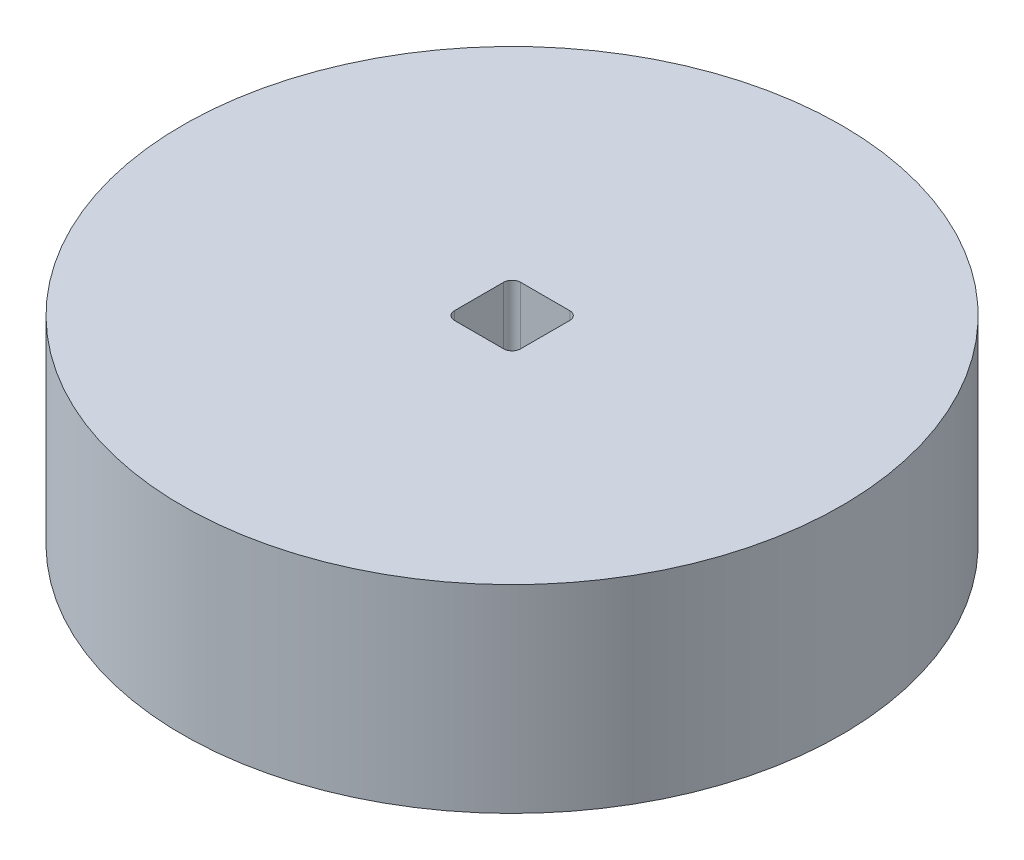
SolidWorks part; units mm, degrees
material "PVC 0.007 塑化"
ref_plane "前视基准面" through (0, 0, 0) normal (0, 0, 1) x (1, 0, 0)
ref_plane "上视基准面" through (0, 0, 0) normal (0, 1, 0) x (1, 0, 0)
ref_plane "右视基准面" through (0, 0, 0) normal (1, 0, 0) x (0, 0, -1)
other "Configuration Table"
sketch "草图1" plane through (0, 0, 0) normal (0, 1, 0) x (1, 0, 0)
  circle A0 centre (0, 0) radius 34.925
  line B0 (-2.6013, 3.506) -> (2.6087, 3.506)
  line B1 (2.6087, -3.504) -> (-2.6013, -3.504)
  line B2 (3.5087, -2.604) -> (3.5087, 2.606)
  line B3 (-3.5013, -2.604) -> (-3.5013, 2.606)
  line B4 (3.2451, 3.2424) -> (-3.2377, -3.2404) construction
  arc B5 (-2.6013, 3.506) -> (-3.5013, 2.606) centre (-2.6013, 2.606) ccw
  arc B6 (-3.5013, -2.604) -> (-2.6013, -3.504) centre (-2.6013, -2.604) ccw
  arc B7 (2.6087, -3.504) -> (3.5087, -2.604) centre (2.6087, -2.604) ccw
  arc B8 (3.5087, 2.606) -> (2.6087, 3.506) centre (2.6087, 2.606) ccw
  dimension "D1" = 69.85
sketch_block_instance "块1-3"
sketch_block "块1" parameters "D1"=3.505, "D2"=3.505, "D3"=0.9, "D4"=0.9, "D5"=0.9, "D6"=0.9, "D7"=0.9, "D8"=0.9, "D9"=0.9, "D10"=0.9, "D11"=3.505, "D12"=3.505, "D13"=4.584, "D14"=4.584
extrude "凸台-拉伸1" add sketch "草图1" along normal blind 21 contours A0 | B2 B8 B0 B5 B3 B6 B1 B7
